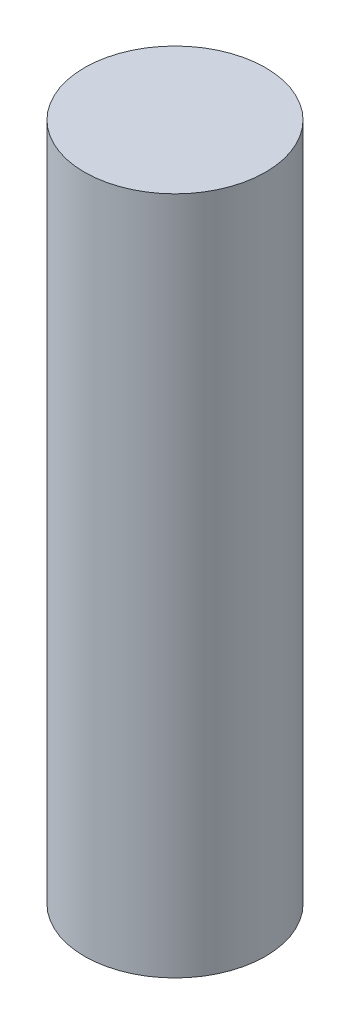
SolidWorks part; units mm, degrees
ref_plane "Front Plane" through (0, 0, 0) normal (0, 0, 1) x (1, 0, 0)
ref_plane "Top Plane" through (0, 0, 0) normal (0, 1, 0) x (1, 0, 0)
ref_plane "Right Plane" through (0, 0, 0) normal (1, 0, 0) x (0, 0, -1)
sketch "Sketch1" plane through (0, 0, 0) normal (0, 1, 0) x (1, 0, 0)
  circle A0 centre (0, 0) radius 4
  dimension "D1" = 8
extrude "Boss-Extrude1" add sketch "Sketch1" along normal blind 30
